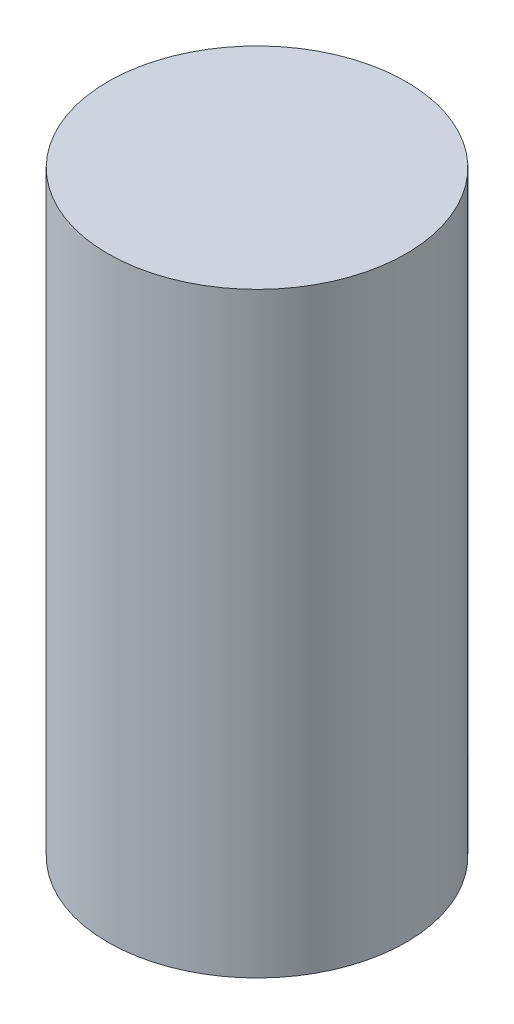
SolidWorks part; units mm, degrees
ref_plane "Front Plane" through (0, 0, 0) normal (0, 0, 1) x (1, 0, 0)
ref_plane "Top Plane" through (0, 0, 0) normal (0, 1, 0) x (1, 0, 0)
ref_plane "Right Plane" through (0, 0, 0) normal (1, 0, 0) x (0, 0, -1)
sketch "Sketch1" plane through (0, 0, 0) normal (0, 1, 0) x (1, 0, 0)
  circle A0 centre (0, 0) radius 2.5
  point P2 (0, 0)
extrude "Boss-Extrude1" add sketch "Sketch1" along normal blind 10
